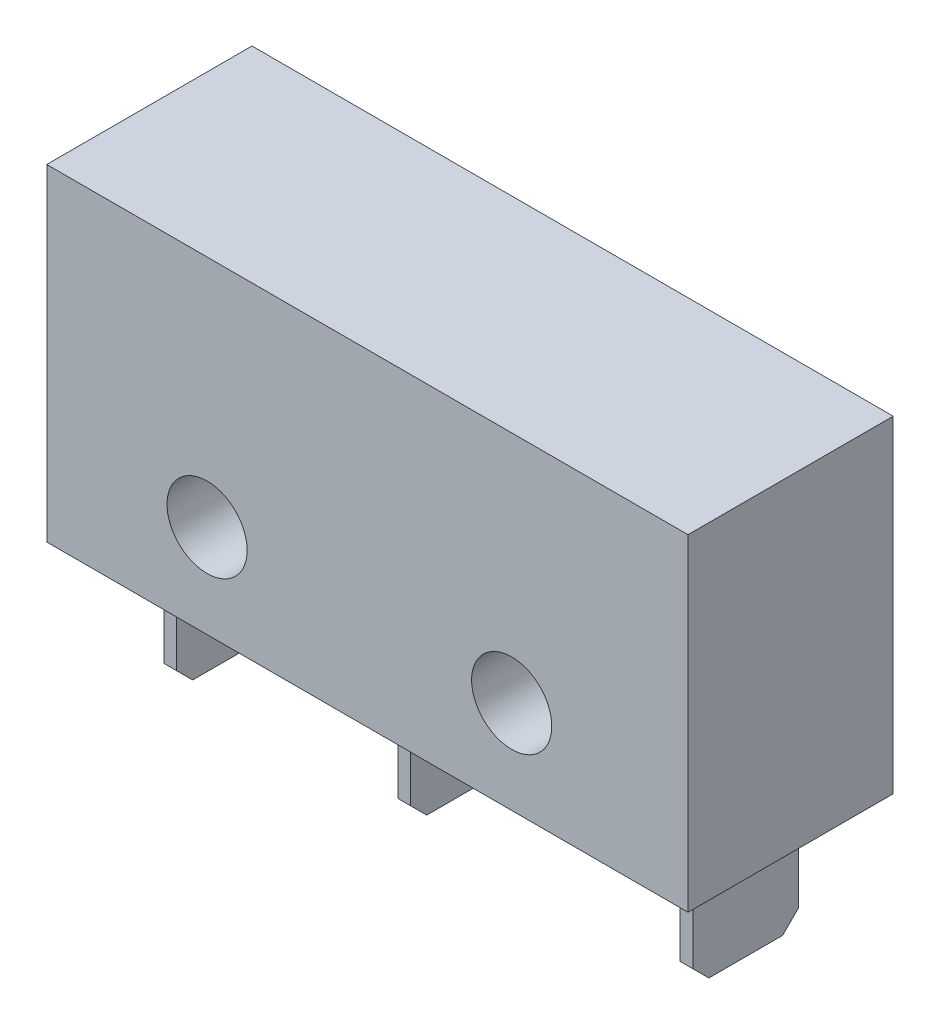
SolidWorks part; units mm, degrees
ref_plane "Front Plane" through (0, 0, 0) normal (0, 0, 1) x (1, 0, 0)
ref_plane "Top Plane" through (0, 0, 0) normal (0, 1, 0) x (1, 0, 0)
ref_plane "Right Plane" through (0, 0, 0) normal (1, 0, 0) x (0, 0, -1)
sketch "Sketch1" plane through (0, 0, 0) normal (0, 0, 1) x (1, 0, 0)
  line L1 (0, 0) -> (20, 0)
  line L2 (0, 0) -> (0, 10.2)
  line L3 (0, 10.2) -> (20, 10.2)
  line L4 (20, 0) -> (20, 10.2)
  dimension "D1" = 20
  dimension "D2" = 10.2
extrude "Boss-Extrude1" add sketch "Sketch1" along normal blind 6.4
sketch "Sketch2" plane through (0, 0, 0) normal (0, -1, 0) x (1, 0, 0)
  line L0 (0, 3.2) -> (20, 3.2) construction
  line L2 (18.2, 4.85) -> (18.6, 4.85)
  line L3 (18.2, 4.85) -> (18.2, 1.55)
  line L4 (0, 0) -> (20, 0)
  line L5 (20, 0) -> (20, 6.4)
  line L6 (20, 6.4) -> (0, 6.4)
  line L7 (0, 6.4) -> (0, 0)
  line L8 (0, 0) -> (20, 0) construction
  line L9 (20, 0) -> (20, 6.4) construction
  line L10 (20, 6.4) -> (0, 6.4) construction
  line L11 (0, 6.4) -> (0, 0) construction
  line L12 (18.2, 1.55) -> (18.6, 1.55)
  line L13 (18.6, 4.85) -> (18.6, 1.55)
  line L14 (9.4, 4.85) -> (9.8, 4.85)
  line L15 (9.4, 4.85) -> (9.4, 1.55)
  line L16 (9.4, 1.55) -> (9.8, 1.55)
  line L17 (9.8, 4.85) -> (9.8, 1.55)
  line L18 (2.1, 4.85) -> (2.5, 4.85)
  line L19 (2.1, 4.85) -> (2.1, 1.55)
  line L20 (2.1, 1.55) -> (2.5, 1.55)
  line L21 (2.5, 4.85) -> (2.5, 1.55)
  point P18 (2.1, 3.2)
  point P19 (9.4, 3.2)
  point P20 (18.2, 3.2)
  point P21 (9.6, 1.55)
  point P22 (18.4, 1.55)
  point P23 (2.3, 1.55)
  dimension "D2" = 8.8
  dimension "D3" = 7.3
  dimension "D4" = 0.4
  dimension "D5" = 1.6
  dimension "D6" = 3.3
  dimension "D1" = 0
extrude "Boss-Extrude2" add sketch "Sketch2" along normal blind 3.5
sketch "Sketch3" plane through (0, 0, 6.4) normal (0, 0, 1) x (1, 0, 0)
  line L0 (0, 10.2) -> (0, 0) construction
  line L2 (0, 0) -> (20, 0) construction
  circle A0 centre (14.5, 2.9) radius 1.25
  circle A1 centre (5, 2.9) radius 1.25
  dimension "D4" = 2.5
  dimension "D1" = 14.5
  dimension "D2" = 9.5
  dimension "D3" = 2.9
extrude "Cut-Extrude1" cut sketch "Sketch3" against normal up to next
chamfer "Chamfer1" distance 0.5 angle 45 6 edges at (18.4, -3.5, 4.85) (18.4, -3.5, 1.55) (9.6, -3.5, 4.85) (9.6, -3.5, 1.55) (2.3, -3.5, 1.55) (2.3, -3.5, 4.85)
